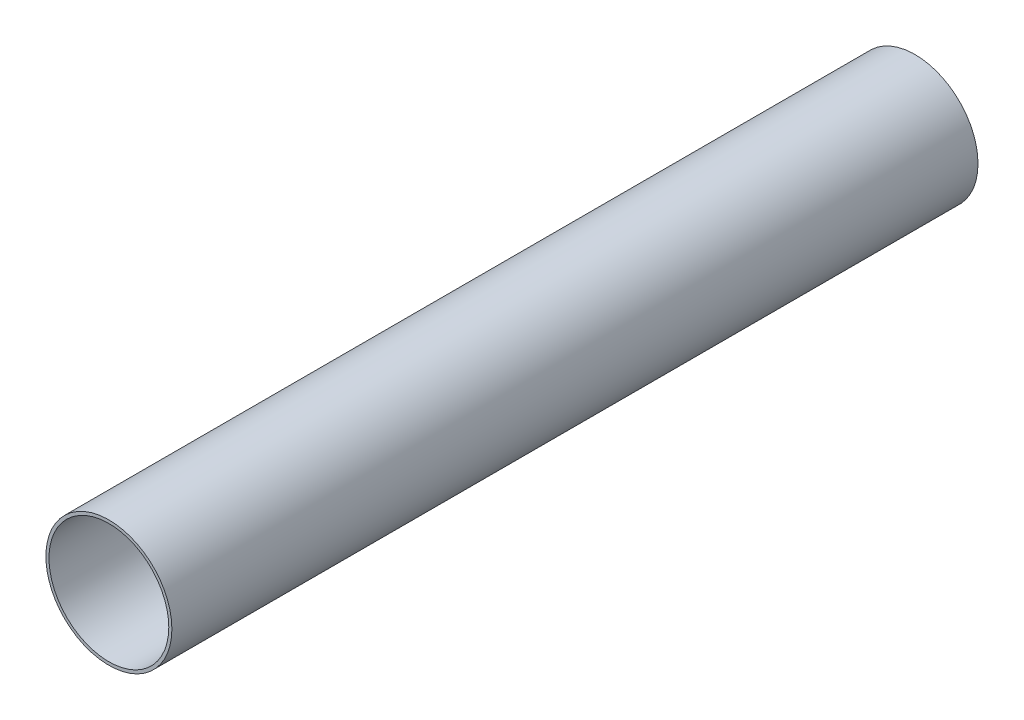
SolidWorks part; units mm, degrees
ref_plane "Plano frontal" through (0, 0, 0) normal (0, 0, 1) x (1, 0, 0)
ref_plane "Plano superior" through (0, 0, 0) normal (0, 1, 0) x (1, 0, 0)
ref_plane "Plano direito" through (0, 0, 0) normal (1, 0, 0) x (0, 0, -1)
sketch "Esboço1" plane through (0, 0, 0) normal (0, 0, 1) x (1, 0, 0)
  circle A0 centre (0, 0) radius 50.8
  circle A1 centre (0, 0) radius 48.3
  dimension "D1" = 101.6
  dimension "D2" = 2.5
extrude "Ressalto-extrusão1" add sketch "Esboço1" along normal blind 650
